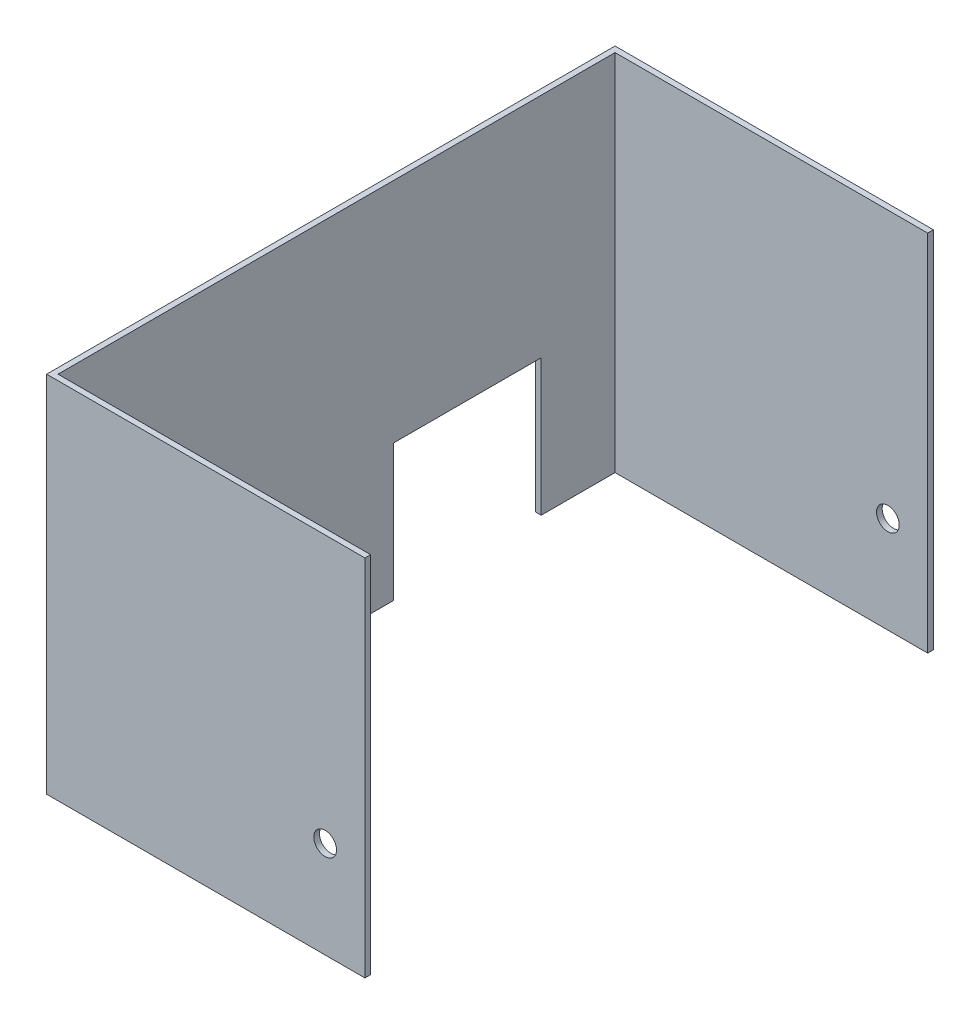
SolidWorks part; units mm, degrees
ref_plane "Front Plane" through (0, 0, 0) normal (0, 0, 1) x (1, 0, 0)
ref_plane "Top Plane" through (0, 0, 0) normal (0, 1, 0) x (1, 0, 0)
ref_plane "Right Plane" through (0, 0, 0) normal (1, 0, 0) x (0, 0, -1)
sketch "Sketch1" plane through (0, 0, 0) normal (0, 1, 0) x (1, 0, 0)
  line L1 (0, 0) -> (355.6, 0)
  line L2 (0, 0) -> (0, 635)
  line L3 (0, 635) -> (355.6, 635)
  line L4 (355.6, 0) -> (355.6, 635)
  dimension "D1" = 355.6
  dimension "D2" = 635
extrude "Boss-Extrude1" add sketch "Sketch1" along normal blind 406.4
shell "Shell1" thickness 6.35
sketch "Sketch2" plane through (6.35, 0, 0) normal (1, 0, 0) x (0, 0, -1)
  line L0 (628.65, 0) -> (6.35, 0) construction
  line L1 (546.1, 0) -> (381, 0)
  line L2 (546.1, 0) -> (546.1, 152.4)
  line L3 (546.1, 152.4) -> (381, 152.4)
  line L4 (381, 0) -> (381, 152.4)
  line L5 (635, 406.4) -> (635, 0) construction
  dimension "D1" = 165.1
  dimension "D2" = 152.4
  dimension "D3" = 88.9
extrude "Cut-Extrude1" cut sketch "Sketch2" against normal through all
sketch "Sketch3" plane through (0, 0, 0) normal (0, 0, 1) x (1, 0, 0)
  line L0 (0, 0) -> (355.6, 0) construction
  line L1 (355.6, 406.4) -> (355.6, 0) construction
  circle A0 centre (311.15, 107.95) radius 12.7
  dimension "D1" = 25.4
  dimension "D2" = 107.95
  dimension "D3" = 44.45
extrude "Cut-Extrude2" cut sketch "Sketch3" against normal through all
